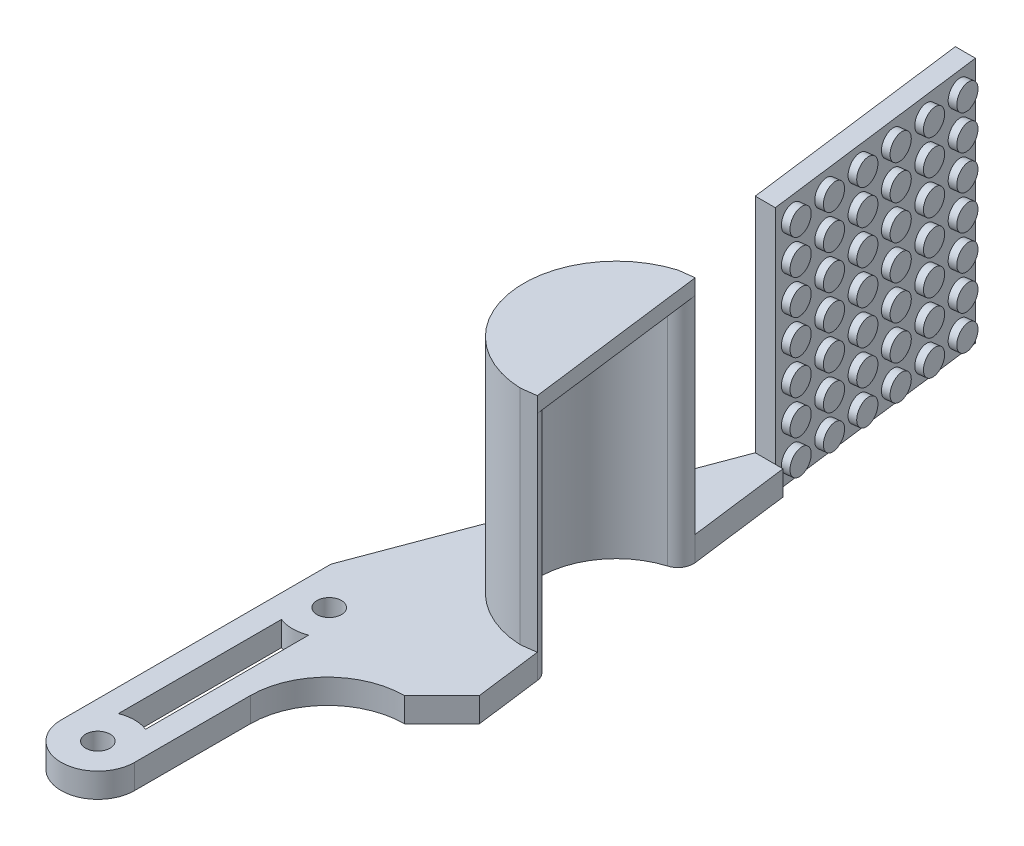
SolidWorks part; units mm, degrees
material "1060-H14"
ref_plane "Alzado" through (0, 0, 0) normal (0, 0, 1) x (1, 0, 0)
ref_plane "Planta" through (0, 0, 0) normal (0, 1, 0) x (1, 0, 0)
ref_plane "Vista lateral" through (0, 0, 0) normal (1, 0, 0) x (0, 0, -1)
sketch "Croquis1" plane through (0, 0, 0) normal (0, 1, 0) x (1, 0, 0)
  line L0 (-12.5, 40) -> (12.5, -40) construction
  line L1 (-12.5, 40) -> (12.5, 40) construction
  line L2 (-12.5, 40) -> (-12.5, -40) construction
  line L3 (-12.5, -40) -> (12.5, -40) construction
  line L4 (12.5, 40) -> (12.5, -40) construction
  line L5 (-12.5, 0) -> (-12.5, -40)
  line L6 (-12.5, -40) -> (-2.975, -40)
  line L7 (-2.975, -40) -> (-2.975, -20)
  line L8 (7.025, -10) -> (12.5, -10)
  line L9 (12.5, -10) -> (12.5, 40)
  line L10 (12.5, 40) -> (2.5, 40)
  line L11 (2.5, 40) -> (-12.5, 0)
  circle A0 centre (-7.7375, -5) radius 1.5875
  circle A1 centre (-7.7375, -35) radius 1.5875
  arc A2 (-2.975, -20) -> (7.025, -10) centre (7.025, -20) cw
  dimension "D5" = 3.175
  dimension "D6" = 3.175
  dimension "D12" = 10
  dimension "D1" = 25
  dimension "D2" = 80
  dimension "D3" = 9.525
  dimension "D4" = 30
  dimension "D7" = 4.7625
  dimension "D8" = 5
  dimension "D9" = 10
  dimension "D10" = 40
  dimension "D11" = 50
extrude "Saliente-Extruir1" add sketch "Croquis1" along normal blind 3.175
sketch "Croquis2" plane through (0, 3.175, 0) normal (0, 1, 0) x (1, 0, 0)
  line L0 (12.5, -10) -> (6.1, 40)
  line L1 (12.5, 40) -> (2.5, 40) construction
  line L2 (6.1, 40) -> (12.5, 40)
  line L3 (12.5, 40) -> (12.5, -10)
  dimension "D1" = 6.4
extrude "Cortar-Extruir1" cut sketch "Croquis2" against normal blind 3.175
sketch "Croquis3" plane through (0, 3.175, 0) normal (0, 1, 0) x (1, 0, 0)
  line L1 (-2.975, -40) -> (-2.975, -20) construction
  line L2 (-12.5, -35) -> (-12.5, -40)
  line L3 (-12.5, -40) -> (-2.975, -40)
  line L4 (-2.975, -40) -> (-2.975, -35)
  line L5 (-9.5, -9.4271) -> (-9.5, -30.5756)
  line L6 (-5.975, -14.8038) -> (-5.975, -30.5756)
  line L7 (-12.5, 0) -> (-12.5, -40) construction
  line L8 (-5.975, -14.8038) -> (-5.975, -9.4271)
  line L22 (7.025, -6) -> (7.9554, -6)
  line L23 (7.9554, -6) -> (3.2646, 30.6468)
  line L24 (3.2646, 30.6468) -> (-8.5, -0.7253)
  line L25 (-8.5, -0.7253) -> (-8.5, -36)
  line L26 (-8.5, -36) -> (-6.975, -36)
  line L27 (-6.975, -36) -> (-6.975, -20)
  line L28 (7.025, -6) -> (7.9554, -6)
  arc A2 (-9.5, -9.4271) -> (-5.975, -9.4271) centre (-7.7375, -5) ccw
  arc A3 (-12.5, -35) -> (-2.975, -35) centre (-7.7375, -35) ccw
  arc A4 (-5.975, -30.5756) -> (-9.5, -30.5756) centre (-7.7375, -35) ccw
  arc A6 (7.025, -6) -> (-6.975, -20) centre (7.025, -20) ccw
  dimension "D1" = 9.53
  dimension "D2" = 3
  dimension "D3" = 3
  dimension "D5" = 4
extrude "Cortar-Extruir3" cut sketch "Croquis3" against normal blind 10 contours A4 L6 L8 A2 L5 | A3 L4 L3 L2
sketch "Croquis4" plane through (0, 3.175, 0) normal (0, 1, 0) x (1, 0, 0)
  line L0 (6.1, 40) -> (12.5, -10) construction
  line L1 (7.025, -10) -> (11.8787, -5.1463)
  line L2 (11.8787, -5.1463) -> (12.5, -10)
  line L3 (12.5, -10) -> (7.025, -10)
  circle A0 centre (9.2741, 15.2023) radius 10
  dimension "D1" = 20
  dimension "D2" = 25
  dimension "D3" = 45
extrude "Cortar-Extruir4" cut sketch "Croquis4" against normal blind 10
fillet "Redondeo1" radius 2 2 edges at (8.0045, 1.5875, -25.1214) (10.5437, 1.5875, -5.2832)
sketch "Sketch1" plane through (0, 3.175, 0) normal (0, 1, 0) x (1, 0, 0)
  line L0 (5.788, 26.6848) -> (7.7718, 26.9387)
  line L1 (8.7925, 3.212) -> (10.7764, 3.4659)
  arc A0 (6.369, 24.771) -> (8.8728, 5.2104) centre (9.2741, 15.2023) ccw construction
  arc A1 (6.369, 24.771) -> (8.8728, 5.2104) centre (9.2741, 15.2023) ccw
  arc A2 (6.369, 24.771) -> (7.7718, 26.9387) centre (5.788, 26.6848) ccw construction
  arc A3 (6.369, 24.771) -> (7.7718, 26.9387) centre (5.788, 26.6848) ccw
  arc A4 (10.7764, 3.4659) -> (8.8728, 5.2104) centre (8.7925, 3.212) ccw construction
  arc A5 (10.7764, 3.4659) -> (8.8728, 5.2104) centre (8.7925, 3.212) ccw
  arc A6 (5.788, 26.6848) -> (5.788, 26.6848) centre (5.788, 26.6848) cw
  arc A7 (5.788, 26.6848) -> (8.7925, 3.212) centre (9.2741, 15.2023) ccw
  arc A8 (8.7925, 3.212) -> (8.7925, 3.212) centre (8.7925, 3.212) cw
  dimension "D1" = 2
extrude "Boss-Extrude1" add sketch "Sketch1" along normal blind 26.82
sketch "Sketch2" plane through (0, 29.995, 0) normal (0, 1, 0) x (1, 0, 0)
  line L0 (10.7764, 3.4659) -> (7.7718, 26.9387)
  line L2 (7.7718, 26.9387) -> (5.788, 26.6848)
  line L3 (8.7925, 3.212) -> (10.7764, 3.4659)
  line L4 (7.7718, 26.9387) -> (5.788, 26.6848)
  line L5 (8.7925, 3.212) -> (10.7764, 3.4659)
  arc A4 (5.788, 26.6848) -> (8.7925, 3.212) centre (9.2741, 15.2023) ccw
  arc A5 (10.7764, 3.4659) -> (8.8728, 5.2104) centre (8.7925, 3.212) ccw
  arc A6 (6.369, 24.771) -> (8.8728, 5.2104) centre (9.2741, 15.2023) ccw
  arc A7 (6.369, 24.771) -> (7.7718, 26.9387) centre (5.788, 26.6848) ccw
  arc A8 (5.788, 26.6848) -> (8.7925, 3.212) centre (9.2741, 15.2023) ccw
  dimension "D1" = 0
extrude "Boss-Extrude2" add sketch "Sketch2" along normal blind 2
sketch "Sketch4" plane through (0, 0, 0) normal (0, -1, 0) x (1, 0, 0)
  line L1 (1.2911, -69.7572) -> (-1.3089, -69.7572)
  line L2 (-1.3089, -69.7572) -> (2.5, -40)
  line L3 (6.1, -40) -> (7.7718, -26.9387) construction
  line L4 (6.1, -40) -> (2.5, -40) construction
  line L5 (5.1, -40) -> (2.5, -40)
  line L6 (5.1, -40) -> (1.2911, -69.7572)
  dimension "D1" = 30
  dimension "D2" = 1
extrude "Boss-Extrude3" add sketch "Sketch4" against normal up to surface (31.995 mm away) up to face at (5.8024, 31.995, -14.7579)
sketch "Sketch5" plane through (10.0553, 0, -1.2871) normal (0.9919, 0, -0.127) x (-0.127, 0, -0.9919)
  line L2 (39.0288, 31.995) -> (39.0288, 3.175) construction
  line L3 (69.0288, 31.995) -> (39.0288, 31.995) construction
  circle A0 centre (41.5288, 29.495) radius 1.59
  circle A1 centre (46.5288, 29.495) radius 1.59
  circle A2 centre (51.5288, 29.495) radius 1.59
  circle A3 centre (56.5288, 29.495) radius 1.59
  circle A4 centre (61.5288, 29.495) radius 1.59
  circle A5 centre (66.5288, 29.495) radius 1.59
  circle A6 centre (46.5288, 24.995) radius 1.59
  circle A7 centre (51.5288, 24.995) radius 1.59
  circle A8 centre (56.5288, 24.995) radius 1.59
  circle A9 centre (61.5288, 24.995) radius 1.59
  circle A10 centre (66.5288, 24.995) radius 1.59
  circle A11 centre (46.5288, 20.495) radius 1.59
  circle A12 centre (51.5288, 20.495) radius 1.59
  circle A13 centre (56.5288, 20.495) radius 1.59
  circle A14 centre (61.5288, 20.495) radius 1.59
  circle A15 centre (66.5288, 20.495) radius 1.59
  circle A16 centre (46.5288, 15.995) radius 1.59
  circle A17 centre (51.5288, 15.995) radius 1.59
  circle A18 centre (56.5288, 15.995) radius 1.59
  circle A19 centre (61.5288, 15.995) radius 1.59
  circle A20 centre (66.5288, 15.995) radius 1.59
  circle A21 centre (46.5288, 11.495) radius 1.59
  circle A22 centre (51.5288, 11.495) radius 1.59
  circle A23 centre (56.5288, 11.495) radius 1.59
  circle A24 centre (61.5288, 11.495) radius 1.59
  circle A25 centre (66.5288, 11.495) radius 1.59
  circle A26 centre (46.5288, 6.995) radius 1.59
  circle A27 centre (51.5288, 6.995) radius 1.59
  circle A28 centre (56.5288, 6.995) radius 1.59
  circle A29 centre (61.5288, 6.995) radius 1.59
  circle A30 centre (66.5288, 6.995) radius 1.59
  circle A31 centre (46.5288, 2.495) radius 1.59
  circle A32 centre (51.5288, 2.495) radius 1.59
  circle A33 centre (56.5288, 2.495) radius 1.59
  circle A34 centre (61.5288, 2.495) radius 1.59
  circle A35 centre (66.5288, 2.495) radius 1.59
  circle A36 centre (41.5288, 24.995) radius 1.59
  circle A37 centre (41.5288, 20.495) radius 1.59
  circle A38 centre (41.5288, 15.995) radius 1.59
  circle A39 centre (41.5288, 11.495) radius 1.59
  circle A40 centre (41.5288, 6.995) radius 1.59
  circle A41 centre (41.5288, 2.495) radius 1.59
  dimension "D1" = 3.18
  dimension "D2" = 2.5
  dimension "D3" = 2.5
  dimension "D4" = 6
  dimension "D5" = 7
extrude "Boss-Extrude4" add sketch "Sketch5" along normal blind 1
